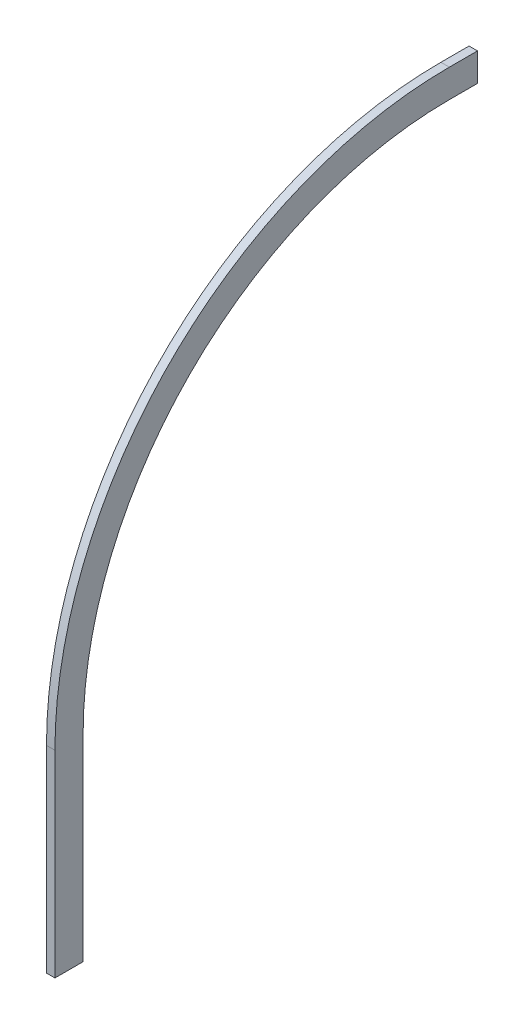
SolidWorks part; units mm, degrees
material "Pine"
ref_plane "Front Plane" through (0, 0, 0) normal (0, 0, 1) x (1, 0, 0)
ref_plane "Top Plane" through (0, 0, 0) normal (0, 1, 0) x (1, 0, 0)
ref_plane "Right Plane" through (0, 0, 0) normal (1, 0, 0) x (0, 0, -1)
sketch "Sketch2" plane through (0, 0, 0) normal (1, 0, 0) x (0, 0, -1)
  line L0 (-10, 0) -> (-10, 70)
  line L2 (0, 0) -> (0, 70)
  line L3 (130, 200) -> (140, 200)
  line L5 (130, 210) -> (140, 210)
  line L6 (140, 210) -> (140, 200)
  line L7 (0, 0) -> (-10, 0)
  arc A0 (130, 200) -> (0, 70) centre (130, 70) ccw
  arc A1 (130, 210) -> (-10, 70) centre (130, 70) ccw
  point P7 (0, 200)
  dimension "D3" = 130
  dimension "D1" = 140
  dimension "D2" = 10
extrude "Boss-Extrude1" add sketch "Sketch2" along normal blind 3
